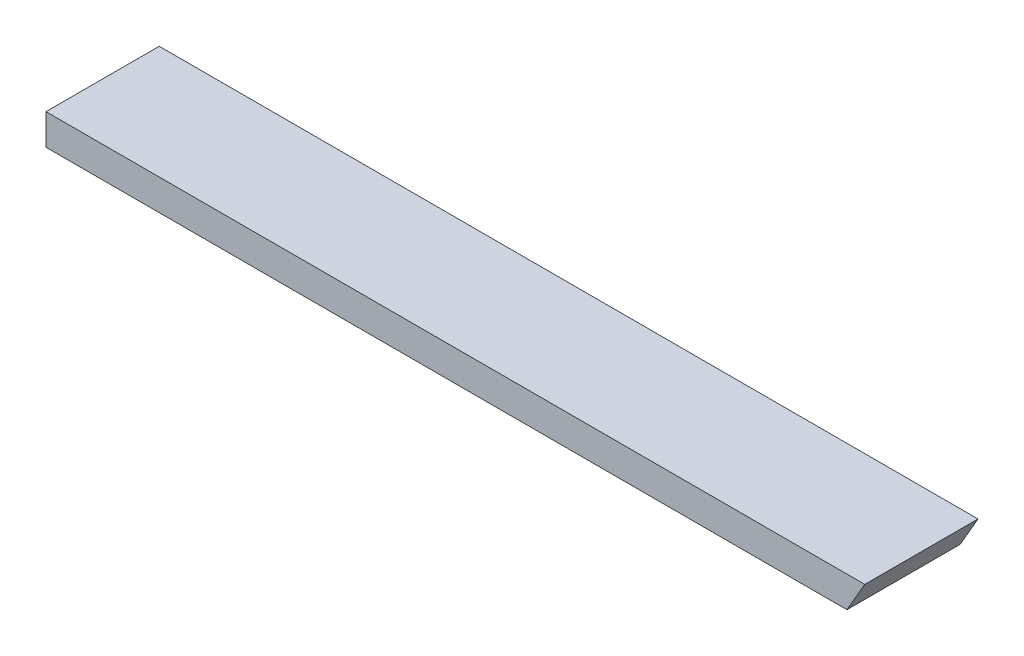
SolidWorks part; units mm, degrees
ref_plane "Front Plane" through (0, 0, 0) normal (0, 0, 1) x (1, 0, 0)
ref_plane "Top Plane" through (0, 0, 0) normal (0, 1, 0) x (1, 0, 0)
ref_plane "Right Plane" through (0, 0, 0) normal (1, 0, 0) x (0, 0, -1)
sketch "Sketch1" plane through (0, 0, 0) normal (0, 1, 0) x (1, 0, 0)
  line L1 (0, 0) -> (1066.8, 0)
  line L2 (0, 0) -> (0, 139.7)
  line L3 (0, 139.7) -> (1066.8, 139.7)
  line L4 (1066.8, 0) -> (1066.8, 139.7)
  dimension "D1" = 139.7
  dimension "D2" = 1066.8
extrude "Boss-Extrude1" add sketch "Sketch1" along normal blind 38.1
sketch "Sketch2" plane through (0, 0, -139.7) normal (0, 0, -1) x (-1, 0, 0)
  line L0 (-988.2822, 0) -> (-1010.2793, 38.1)
  line L3 (-1066.8, 0) -> (0, 0) construction
  line L4 (-1066.8, 38.1) -> (0, 38.1) construction
  line L5 (-1066.8, 38.1) -> (-1066.8, 0) construction
  dimension "D1" = 30
extrude "Cut-Extrude1" cut sketch "Sketch2" against normal through all and the other way through all
